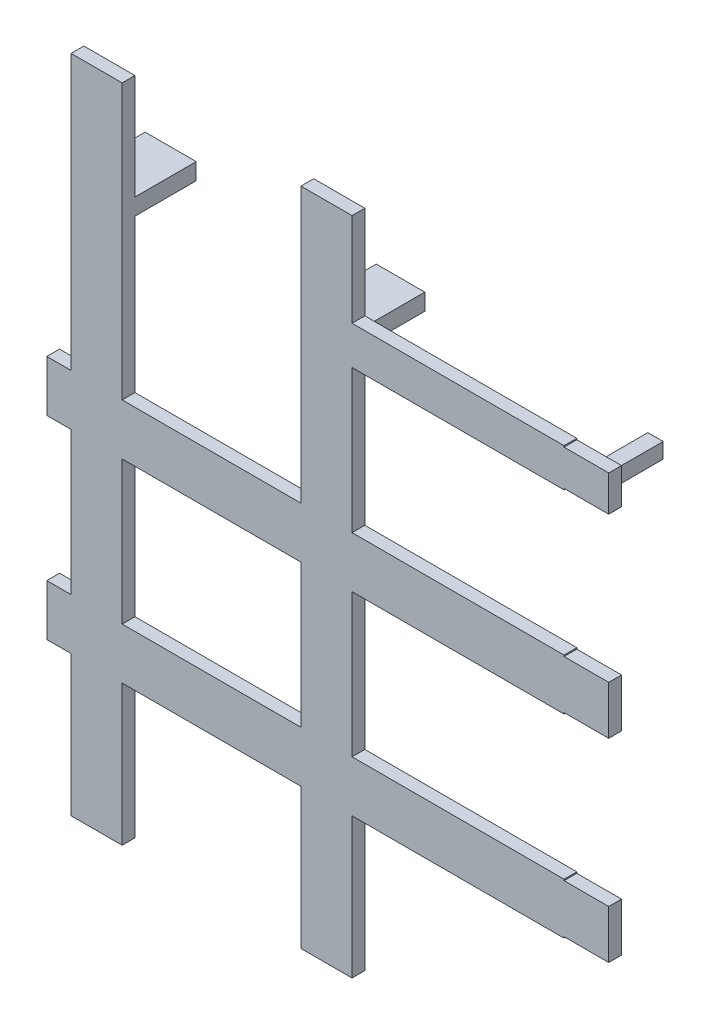
SolidWorks part; units mm, degrees
ref_plane "Piano frontale" through (0, 0, 0) normal (0, 0, 1) x (1, 0, 0)
ref_plane "Piano superiore" through (0, 0, 0) normal (0, 1, 0) x (1, 0, 0)
ref_plane "Piano destro" through (0, 0, 0) normal (1, 0, 0) x (0, 0, -1)
sketch "Schizzo1" plane through (0, 0, 0) normal (0, 0, 1) x (1, 0, 0)
  line L1 (0, 0) -> (4, 0)
  line L2 (0, 0) -> (0, 51.7)
  line L3 (0, 51.7) -> (4, 51.7)
  line L4 (4, 0) -> (4, 51.7)
  dimension "D1" = 4
  dimension "D2" = 51.7
extrude "Estrusione-Estrusione1" add sketch "Schizzo1" along normal blind 1
sketch "Schizzo2" plane through (4, 0, 0) normal (1, 0, 0) x (0, 0, -1)
  line L1 (-1, 0) -> (-1, 51.7) construction
  line L2 (0, 0) -> (0, 51.7) construction
  line L3 (-1, 30.2) -> (0, 30.2)
  line L4 (-1, 30.2) -> (-1, 26.2)
  line L5 (-1, 26.2) -> (0, 26.2)
  line L6 (0, 30.2) -> (0, 26.2)
  dimension "D2" = 4
extrude "Estrusione-Estrusione2" add sketch "Schizzo2" along normal blind 18 and the other way blind 5.9
sketch "Schizzo3" plane through (4, 0, 0) normal (1, 0, 0) x (0, 0, -1)
  line L1 (-1, 0) -> (-1, 26.2) construction
  line L2 (0, 0) -> (0, 26.2) construction
  line L3 (-1, 15) -> (0, 15)
  line L4 (-1, 15) -> (-1, 11)
  line L5 (-1, 11) -> (0, 11)
  line L6 (0, 15) -> (0, 11)
  dimension "D2" = 4
extrude "Estrusione-Estrusione3" add sketch "Schizzo3" along normal blind 18 and the other way blind 5.9
sketch "Schizzo4" plane through (0, 30.2, 0) normal (0, 1, 0) x (1, 0, 0)
  line L0 (4, 0) -> (22, 0) construction
  line L1 (22, -1) -> (18, -1)
  line L2 (22, -1) -> (22, 0)
  line L3 (22, 0) -> (18, 0)
  line L4 (18, -1) -> (18, 0)
  dimension "D1" = 4
extrude "Estrusione-Estrusione4" add sketch "Schizzo4" along normal blind 21.5 and the other way blind 30.2
sketch "Schizzo5" plane through (22, 0, 0) normal (1, 0, 0) x (0, 0, -1)
  line L0 (0, 0) -> (0, 51.7) construction
  line L1 (0, 44.3987) -> (-1, 44.3987)
  line L2 (0, 44.3987) -> (0, 41.3987)
  line L3 (0, 41.3987) -> (-1, 41.3987)
  line L4 (-1, 44.3987) -> (-1, 41.3987)
  line L5 (-1, 51.7) -> (-1, 0) construction
  dimension "D1" = 3
extrude "Estrusione-Estrusione5" add sketch "Schizzo5" along normal blind 21
sketch "Schizzo7" plane through (22, 0, 0) normal (1, 0, 0) x (0, 0, -1)
  line L1 (-1, 41.3987) -> (-1, 0) construction
  line L2 (0, 0) -> (0, 41.3987) construction
  line L3 (-1, 11) -> (0, 11)
  line L4 (-1, 11) -> (-1, 15)
  line L5 (-1, 15) -> (0, 15)
  line L6 (0, 11) -> (0, 15)
  dimension "D2" = 4
extrude "Estrusione-Estrusione6" add sketch "Schizzo7" along normal blind 21
sketch "Schizzo8" plane through (22, 0, 0) normal (1, 0, 0) x (0, 0, -1)
  line L1 (-1, 41.3987) -> (-1, 15) construction
  line L2 (0, 15) -> (0, 41.3987) construction
  line L3 (-1, 26.2) -> (0, 26.2)
  line L4 (-1, 26.2) -> (-1, 30.2)
  line L5 (-1, 30.2) -> (0, 30.2)
  line L6 (0, 26.2) -> (0, 30.2)
  dimension "D2" = 4
extrude "Estrusione-Estrusione7" add sketch "Schizzo8" along normal blind 21
sketch "Schizzo10" plane through (0, 0, 0) normal (0, 0, -1) x (-1, 0, 0)
  line L1 (-4, 30.2) -> (-4, 51.7) construction
  line L2 (0, 51.7) -> (0, 30.2) construction
  line L3 (-4, 42.16) -> (0, 42.16)
  line L4 (-4, 42.16) -> (-4, 43.46)
  line L5 (-4, 43.46) -> (0, 43.46)
  line L6 (0, 42.16) -> (0, 43.46)
  dimension "D2" = 1.3
extrude "Estrusione-Estrusione9" add sketch "Schizzo10" along normal blind 4.8
sketch "Schizzo11" plane through (0, 0, 0) normal (0, 0, -1) x (-1, 0, 0)
  line L1 (-18, 30.2) -> (-18, 51.7) construction
  line L3 (-18, 42.26) -> (-21.9, 42.26)
  line L4 (-18, 42.26) -> (-18, 43.56)
  line L5 (-18, 43.56) -> (-21.9, 43.56)
  line L6 (-21.9, 42.26) -> (-21.9, 43.56)
  dimension "D2" = 3.9
  dimension "D3" = 1.3
extrude "Estrusione-Estrusione10" add sketch "Schizzo11" along normal blind 4.8
sketch "Schizzo12" plane through (0, 0, 0) normal (0, 0, -1) x (-1, 0, 0)
  line L4 (-41.3654, 43.566) -> (-40.1654, 43.566)
  line L5 (-41.3654, 43.566) -> (-41.3654, 42.366)
  line L6 (-41.3654, 42.366) -> (-40.1654, 42.366)
  line L7 (-40.1654, 43.566) -> (-40.1654, 42.366)
  dimension "D3" = 1.2
  dimension "D4" = 1.2
extrude "Estrusione-Estrusione11" add sketch "Schizzo12" along normal blind 4
sketch "Schizzo13" plane through (43, 0, 0) normal (1, 0, 0) x (0, 0, -1)
  line L1 (-1, 30.2) -> (0, 30.2)
  line L2 (-1, 30.2) -> (-1, 26.2)
  line L3 (-1, 26.2) -> (0, 26.2)
  line L4 (0, 30.2) -> (0, 26.2)
extrude "Taglio-Estrusione1" cut sketch "Schizzo13" against normal blind 0.9
sketch "Schizzo14" plane through (43, 0, 0) normal (1, 0, 0) x (0, 0, -1)
  line L0 (0, 11) -> (0, 15) construction
  line L1 (-1, 15) -> (0, 15)
  line L2 (-1, 15) -> (-1, 11)
  line L3 (-1, 11) -> (0, 11)
  line L4 (0, 15) -> (0, 11)
extrude "Taglio-Estrusione2" cut sketch "Schizzo14" against normal blind 0.9
sketch "Schizzo15" plane through (43, 0, 0) normal (1, 0, 0) x (0, 0, -1)
  line L0 (-1, 41.3987) -> (0, 41.3987) construction
  line L1 (-1, 44.3987) -> (0, 44.3987)
  line L2 (-1, 44.3987) -> (-1, 41.3987)
  line L3 (-1, 41.3987) -> (0, 41.3987)
  line L4 (0, 44.3987) -> (0, 41.3987)
extrude "Taglio-Estrusione3" cut sketch "Schizzo15" against normal blind 0.9
sketch "Schizzo16" plane through (0, 11, 0) normal (0, -1, 0) x (1, 0, 0)
  line L0 (42.1, 0) -> (22, 0) construction
  line L1 (42.1, 1) -> (38.5964, 1)
  line L2 (42.1, 1) -> (42.1, 0)
  line L3 (42.1, 0) -> (38.5964, 0)
  line L4 (38.5964, 1) -> (38.5964, 0)
extrude "Taglio-Estrusione4" cut sketch "Schizzo16" against normal blind 0.1
sketch "Schizzo17" plane through (0, 15, 0) normal (0, 1, 0) x (1, 0, 0)
  line L0 (42.1, -1) -> (22, -1) construction
  line L1 (42.1, 0) -> (38.6, 0)
  line L2 (42.1, 0) -> (42.1, -1)
  line L3 (42.1, -1) -> (38.6, -1)
  line L4 (38.6, 0) -> (38.6, -1)
  dimension "D1" = 3.5
extrude "Taglio-Estrusione5" cut sketch "Schizzo17" against normal blind 0.1
sketch "Schizzo18" plane through (0, 30.2, 0) normal (0, 1, 0) x (1, 0, 0)
  line L0 (42.1, -1) -> (22, -1) construction
  line L1 (42.1, 0) -> (38.6, 0)
  line L2 (42.1, 0) -> (42.1, -1)
  line L3 (42.1, -1) -> (38.6, -1)
  line L4 (38.6, 0) -> (38.6, -1)
  dimension "D1" = 3.5
extrude "Taglio-Estrusione6" cut sketch "Schizzo18" against normal blind 0.1
sketch "Schizzo19" plane through (0, 26.2, 0) normal (0, -1, 0) x (-1, 0, 0)
  line L0 (-42.1, 0) -> (-22, 0) construction
  line L1 (-42.1, -1) -> (-38.6, -1)
  line L2 (-42.1, -1) -> (-42.1, 0)
  line L3 (-42.1, 0) -> (-38.6, 0)
  line L4 (-38.6, -1) -> (-38.6, 0)
  dimension "D1" = 3.5
extrude "Taglio-Estrusione7" cut sketch "Schizzo19" against normal blind 0.1
sketch "Schizzo20" plane through (0, 41.3987, 0) normal (0, -1, 0) x (-1, 0, 0)
  line L0 (-42.1, 0) -> (-22, 0) construction
  line L1 (-42.1, -1) -> (-38.6, -1)
  line L2 (-42.1, -1) -> (-42.1, 0)
  line L3 (-42.1, 0) -> (-38.6, 0)
  line L4 (-38.6, -1) -> (-38.6, 0)
  dimension "D1" = 3.5
extrude "Taglio-Estrusione8" cut sketch "Schizzo20" against normal blind 0.1
sketch "Schizzo21" plane through (0, 44.3987, 0) normal (0, 1, 0) x (1, 0, 0)
  line L0 (42.1, 0) -> (22, 0) construction
  line L1 (42.1, -1) -> (38.6, -1)
  line L2 (42.1, -1) -> (42.1, 0)
  line L3 (42.1, 0) -> (38.6, 0)
  line L4 (38.6, -1) -> (38.6, 0)
  dimension "D1" = 3.5
extrude "Taglio-Estrusione9" cut sketch "Schizzo21" against normal blind 0.1
sketch "Schizzo22" plane through (0, 0, -4.8) normal (0, 0, -1) x (-1, 0, 0)
  line L0 (-21.9, 42.26) -> (-18, 42.26) construction
  line L1 (-18, 43.56) -> (-18.0982, 43.56)
  line L2 (-18, 43.56) -> (-18, 42.26)
  line L3 (-18, 42.26) -> (-18.0982, 42.26)
  line L4 (-18.0982, 43.56) -> (-18.0982, 42.26)
extrude "Taglio-Estrusione10" cut sketch "Schizzo22" against normal blind 4.8
